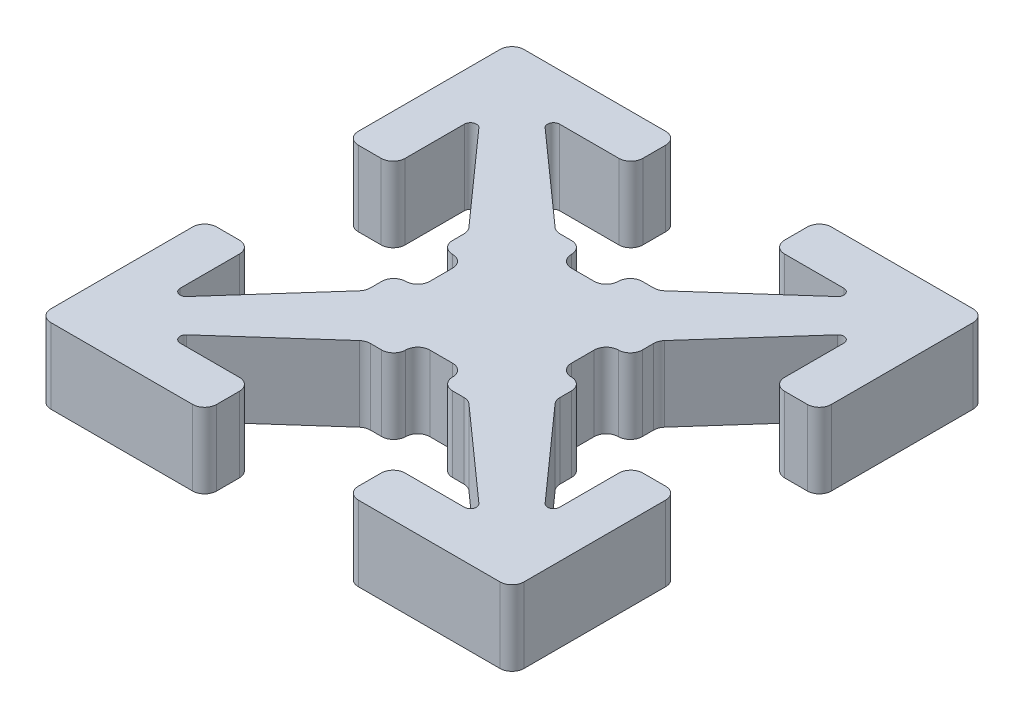
SolidWorks part; units mm, degrees
material "6063-T6"
ref_plane "Front Plane" through (0, 0, 0) normal (0, 0, 1) x (1, 0, 0)
ref_plane "Top Plane" through (0, 0, 0) normal (0, 1, 0) x (1, 0, 0)
ref_plane "Right Plane" through (0, 0, 0) normal (1, 0, 0) x (0, 0, -1)
sketch "Sketch1" plane through (0, 0, 0) normal (0, 1, 0) x (1, 0, 0)
  line L0 (-1.1595, 2.0709) -> (-3.0909, 3.7914)
  line L1 (-0.7493, 2.0066) -> (-0.9906, 2.0066)
  line L2 (-1.4986, 4.2672) -> (-1.4986, 4.7498)
  line L3 (-1.7526, 4.0132) -> (-3.0064, 4.0132)
  line L4 (-1.7526, 5.0038) -> (-4.7498, 5.0038)
  line L5 (-0.2413, 1.4986) -> (0.2413, 1.4986)
  line L6 (-5.0038, 5.0038) -> (5.0038, -5.0038) construction
  line L7 (-1.4986, 0.2413) -> (-1.4986, -0.2413)
  line L8 (-5.0038, 1.7526) -> (-5.0038, 4.7498)
  line L9 (-4.0132, 1.7526) -> (-4.0132, 3.0064)
  line L10 (-4.2672, 1.4986) -> (-4.7498, 1.4986)
  line L11 (-2.0066, 0.7493) -> (-2.0066, 0.9906)
  line L12 (0, 5.0038) -> (0, -5.0038) construction
  line L13 (5.0038, 0) -> (-5.0038, 0) construction
  line L14 (-2.0709, 1.1595) -> (-3.7914, 3.0909)
  line L15 (2.0709, 1.1595) -> (3.7914, 3.0909)
  line L16 (2.0066, 0.7493) -> (2.0066, 0.9906)
  line L17 (4.2672, 1.4986) -> (4.7498, 1.4986)
  line L18 (4.0132, 1.7526) -> (4.0132, 3.0064)
  line L19 (5.0038, 1.7526) -> (5.0038, 4.7498)
  line L20 (1.4986, 0.2413) -> (1.4986, -0.2413)
  line L21 (1.7526, 5.0038) -> (4.7498, 5.0038)
  line L22 (1.7526, 4.0132) -> (3.0064, 4.0132)
  line L23 (1.4986, 4.2672) -> (1.4986, 4.7498)
  line L24 (0.7493, 2.0066) -> (0.9906, 2.0066)
  line L25 (1.1595, 2.0709) -> (3.0909, 3.7914)
  line L26 (1.1595, -2.0709) -> (3.0909, -3.7914)
  line L27 (0.7493, -2.0066) -> (0.9906, -2.0066)
  line L28 (1.4986, -4.2672) -> (1.4986, -4.7498)
  line L29 (1.7526, -4.0132) -> (3.0064, -4.0132)
  line L30 (1.7526, -5.0038) -> (4.7498, -5.0038)
  line L31 (5.0038, -1.7526) -> (5.0038, -4.7498)
  line L32 (4.0132, -1.7526) -> (4.0132, -3.0064)
  line L33 (4.2672, -1.4986) -> (4.7498, -1.4986)
  line L34 (2.0066, -0.7493) -> (2.0066, -0.9906)
  line L35 (2.0709, -1.1595) -> (3.7914, -3.0909)
  line L36 (-2.0709, -1.1595) -> (-3.7914, -3.0909)
  line L37 (-2.0066, -0.7493) -> (-2.0066, -0.9906)
  line L38 (-4.2672, -1.4986) -> (-4.7498, -1.4986)
  line L39 (-4.0132, -1.7526) -> (-4.0132, -3.0064)
  line L40 (-5.0038, -1.7526) -> (-5.0038, -4.7498)
  line L41 (-0.2413, -1.4986) -> (0.2413, -1.4986)
  line L42 (-1.7526, -5.0038) -> (-4.7498, -5.0038)
  line L43 (-1.7526, -4.0132) -> (-3.0064, -4.0132)
  line L44 (-1.4986, -4.2672) -> (-1.4986, -4.7498)
  line L45 (-0.7493, -2.0066) -> (-0.9906, -2.0066)
  line L46 (-1.1595, -2.0709) -> (-3.0909, -3.7914)
  arc A0 (-4.0132, 3.0064) -> (-3.7914, 3.0909) centre (-3.8862, 3.0064) cw
  arc A1 (-1.7526, 0.4953) -> (-2.0066, 0.7493) centre (-1.7526, 0.7493) cw
  arc A2 (-2.0066, 0.9906) -> (-2.0709, 1.1595) centre (-2.2606, 0.9906) ccw
  arc A3 (-4.0132, 1.7526) -> (-4.2672, 1.4986) centre (-4.2672, 1.7526) cw
  arc A4 (-4.7498, 1.4986) -> (-5.0038, 1.7526) centre (-4.7498, 1.7526) cw
  arc A5 (-1.4986, 0.2413) -> (-1.7526, 0.4953) centre (-1.7526, 0.2413) ccw
  arc A6 (-0.2413, 1.4986) -> (-0.4953, 1.7526) centre (-0.2413, 1.7526) cw
  arc A7 (-1.4986, 4.7498) -> (-1.7526, 5.0038) centre (-1.7526, 4.7498) ccw
  arc A8 (-1.7526, 4.0132) -> (-1.4986, 4.2672) centre (-1.7526, 4.2672) ccw
  arc A9 (-0.9906, 2.0066) -> (-1.1595, 2.0709) centre (-0.9906, 2.2606) cw
  arc A10 (-0.4953, 1.7526) -> (-0.7493, 2.0066) centre (-0.7493, 1.7526) ccw
  arc A11 (-3.0064, 4.0132) -> (-3.0909, 3.7914) centre (-3.0064, 3.8862) ccw
  arc A12 (4.7498, 5.0038) -> (5.0038, 4.7498) centre (4.7498, 4.7498) cw
  arc A13 (3.0064, 4.0132) -> (3.0909, 3.7914) centre (3.0064, 3.8862) cw
  arc A14 (0.4953, 1.7526) -> (0.7493, 2.0066) centre (0.7493, 1.7526) cw
  arc A15 (0.9906, 2.0066) -> (1.1595, 2.0709) centre (0.9906, 2.2606) ccw
  arc A16 (1.7526, 4.0132) -> (1.4986, 4.2672) centre (1.7526, 4.2672) cw
  arc A17 (1.4986, 4.7498) -> (1.7526, 5.0038) centre (1.7526, 4.7498) cw
  arc A18 (0.2413, 1.4986) -> (0.4953, 1.7526) centre (0.2413, 1.7526) ccw
  arc A19 (1.4986, 0.2413) -> (1.7526, 0.4953) centre (1.7526, 0.2413) cw
  arc A20 (4.7498, 1.4986) -> (5.0038, 1.7526) centre (4.7498, 1.7526) ccw
  arc A21 (4.0132, 1.7526) -> (4.2672, 1.4986) centre (4.2672, 1.7526) ccw
  arc A22 (2.0066, 0.9906) -> (2.0709, 1.1595) centre (2.2606, 0.9906) cw
  arc A23 (1.7526, 0.4953) -> (2.0066, 0.7493) centre (1.7526, 0.7493) ccw
  arc A24 (4.0132, 3.0064) -> (3.7914, 3.0909) centre (3.8862, 3.0064) ccw
  arc A25 (-4.7498, -5.0038) -> (-5.0038, -4.7498) centre (-4.7498, -4.7498) cw
  arc A26 (4.0132, -3.0064) -> (3.7914, -3.0909) centre (3.8862, -3.0064) cw
  arc A27 (1.7526, -0.4953) -> (2.0066, -0.7493) centre (1.7526, -0.7493) cw
  arc A28 (2.0066, -0.9906) -> (2.0709, -1.1595) centre (2.2606, -0.9906) ccw
  arc A29 (4.0132, -1.7526) -> (4.2672, -1.4986) centre (4.2672, -1.7526) cw
  arc A30 (4.7498, -1.4986) -> (5.0038, -1.7526) centre (4.7498, -1.7526) cw
  arc A31 (1.4986, -0.2413) -> (1.7526, -0.4953) centre (1.7526, -0.2413) ccw
  arc A32 (0.2413, -1.4986) -> (0.4953, -1.7526) centre (0.2413, -1.7526) cw
  arc A33 (1.4986, -4.7498) -> (1.7526, -5.0038) centre (1.7526, -4.7498) ccw
  arc A34 (1.7526, -4.0132) -> (1.4986, -4.2672) centre (1.7526, -4.2672) ccw
  arc A35 (0.9906, -2.0066) -> (1.1595, -2.0709) centre (0.9906, -2.2606) cw
  arc A36 (0.4953, -1.7526) -> (0.7493, -2.0066) centre (0.7493, -1.7526) ccw
  arc A37 (3.0064, -4.0132) -> (3.0909, -3.7914) centre (3.0064, -3.8862) ccw
  arc A38 (4.7498, -5.0038) -> (5.0038, -4.7498) centre (4.7498, -4.7498) ccw
  arc A39 (-3.0064, -4.0132) -> (-3.0909, -3.7914) centre (-3.0064, -3.8862) cw
  arc A40 (-0.4953, -1.7526) -> (-0.7493, -2.0066) centre (-0.7493, -1.7526) cw
  arc A41 (-0.9906, -2.0066) -> (-1.1595, -2.0709) centre (-0.9906, -2.2606) ccw
  arc A42 (-1.7526, -4.0132) -> (-1.4986, -4.2672) centre (-1.7526, -4.2672) cw
  arc A43 (-1.4986, -4.7498) -> (-1.7526, -5.0038) centre (-1.7526, -4.7498) cw
  arc A44 (-0.2413, -1.4986) -> (-0.4953, -1.7526) centre (-0.2413, -1.7526) ccw
  arc A45 (-1.4986, -0.2413) -> (-1.7526, -0.4953) centre (-1.7526, -0.2413) cw
  arc A46 (-4.7498, -1.4986) -> (-5.0038, -1.7526) centre (-4.7498, -1.7526) ccw
  arc A47 (-4.0132, -1.7526) -> (-4.2672, -1.4986) centre (-4.2672, -1.7526) ccw
  arc A48 (-2.0066, -0.9906) -> (-2.0709, -1.1595) centre (-2.2606, -0.9906) cw
  arc A49 (-1.7526, -0.4953) -> (-2.0066, -0.7493) centre (-1.7526, -0.7493) ccw
  arc A50 (-4.0132, -3.0064) -> (-3.7914, -3.0909) centre (-3.8862, -3.0064) ccw
  arc A51 (-4.7498, 5.0038) -> (-5.0038, 4.7498) centre (-4.7498, 4.7498) ccw
  point P0 (0, 0)
  point P81 (-1.4986, 0)
  point P82 (0, 1.4986)
  point P156 (1.4986, 0)
  dimension "D1" = 5.0038
  dimension "D2" = 0.9906
  dimension "D3" = 1.4986
  dimension "D8" = 0.254
  dimension "D9" = 0.127
  dimension "D5" = 0.508
  dimension "D6" = 1.4986
  dimension "D7" = 0.4953
  dimension "D10" = 0.4953
  dimension "D11" = 0.9906
extrude "Boss-Extrude1" add sketch "Sketch1" along normal blind 1.5875
